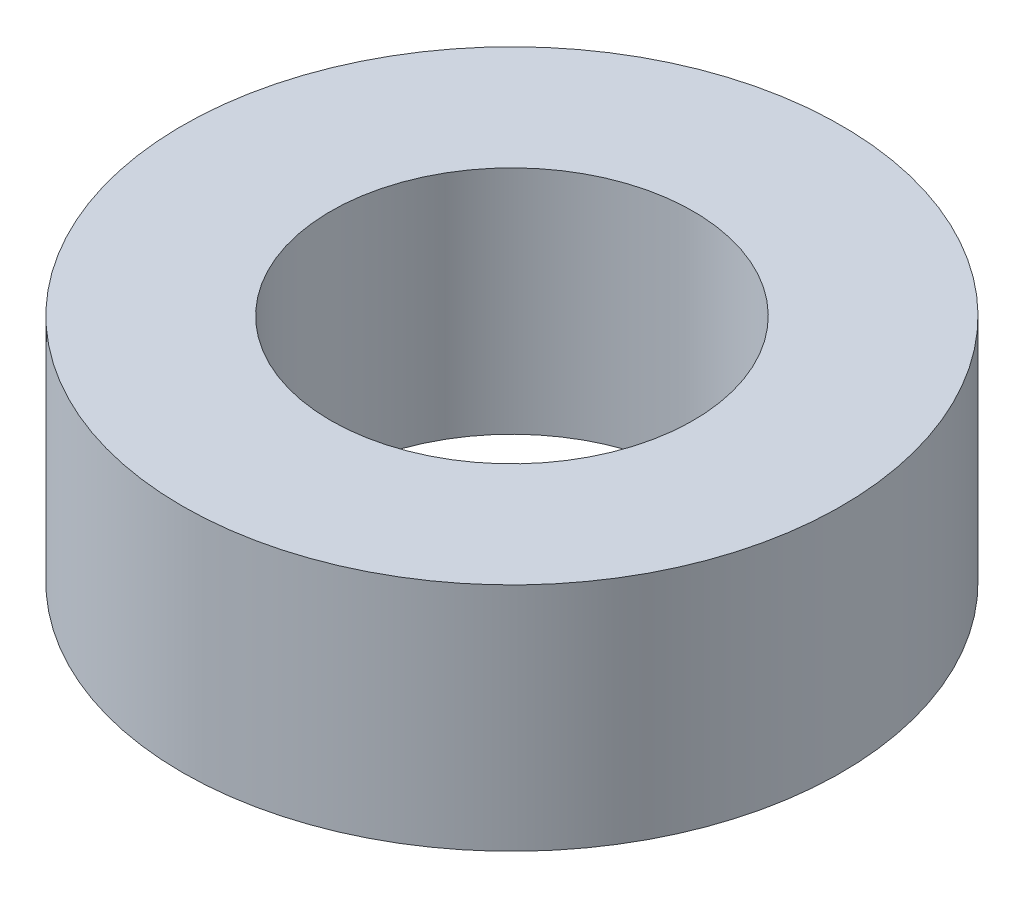
SolidWorks part; units mm, degrees
ref_plane "Front Plane" through (0, 0, 0) normal (0, 0, 1) x (1, 0, 0)
ref_plane "Top Plane" through (0, 0, 0) normal (0, 1, 0) x (1, 0, 0)
ref_plane "Right Plane" through (0, 0, 0) normal (1, 0, 0) x (0, 0, -1)
sketch "Sketch1" plane through (0, 0, 0) normal (0, 1, 0) x (1, 0, 0)
  circle A0 centre (0, 0) radius 1.65
  circle A1 centre (0, 0) radius 3
extrude "Boss-Extrude1" add sketch "Sketch1" along normal blind 2.1
